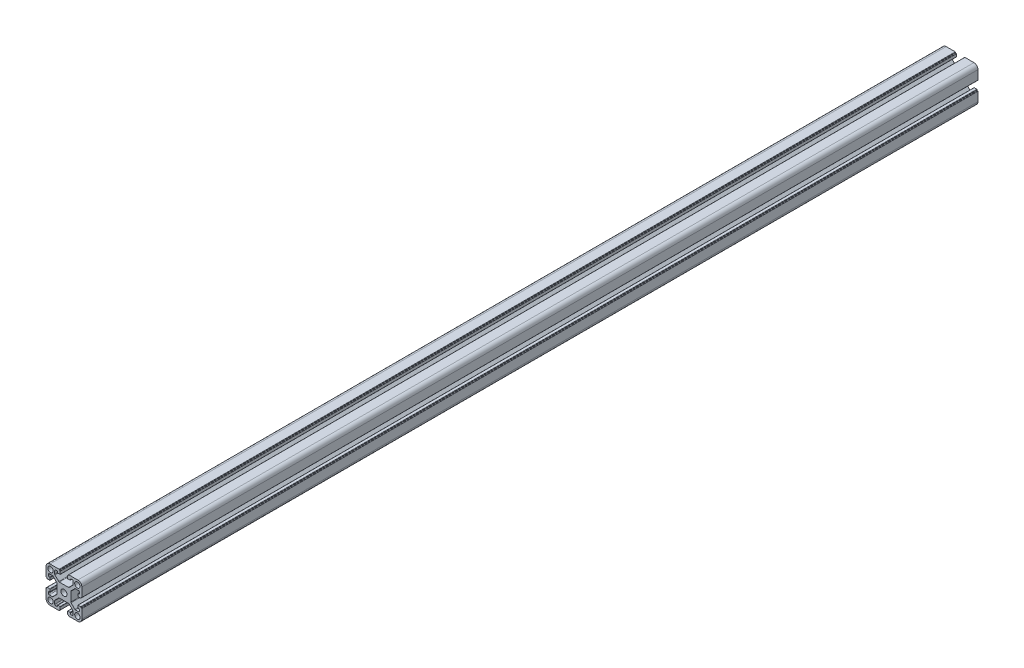
SolidWorks part; units mm, degrees
material "6063 T5"
ref_plane "Спереди" through (0, 0, 0) normal (0, 0, 1) x (1, 0, 0)
ref_plane "Сверху" through (0, 0, 0) normal (0, 1, 0) x (1, 0, 0)
ref_plane "Справа" through (0, 0, 0) normal (1, 0, 0) x (0, 0, -1)
sketch "Эскиз1" plane through (0, 0, 0) normal (0, 0, 1) x (1, 0, 0)
  line L0 (-19.98, 20.5457) -> (20.02, 20.5457) construction
  line L1 (-20, 10.25) -> (-20, 15.5)
  line L2 (-15.5, 20) -> (-10.25, 20)
  line L3 (10.25, 20) -> (15.5, 20)
  line L8 (20, 15.5) -> (20, 10.25)
  line L13 (20, -10.25) -> (20, -15.5)
  line L14 (15.5, -20) -> (10.25, -20)
  line L19 (-10.25, -20) -> (-15.5, -20)
  line L20 (-20, -15.5) -> (-20, -10.25)
  line L26 (-20.0124, 26.0326) -> (19.9876, 26.0326) construction
  arc A0 (-20, 15.5) -> (-15.5, 20) centre (-15.5, 15.5) cw
  circle A5 centre (0, 0) radius 3.4
  arc A6 (15.5, 20) -> (20, 15.5) centre (15.5, 15.5) cw
  circle A11 centre (15, 15) radius 3
  arc A16 (20, -15.5) -> (15.5, -20) centre (15.5, -15.5) cw
  circle A33 centre (-15, 15) radius 3
  circle A34 centre (15, -15) radius 3
  arc A35 (-15.5, -20) -> (-20, -15.5) centre (-15.5, -15.5) cw
  circle A36 centre (-15, -15) radius 3
  point P5 (0, 0)
  point P38 (0, 0)
  line B0 (-20, 10.25) -> (-20, 5.4)
  line B1 (-19.7, 5.1) -> (-19.3, 5.1)
  line B2 (-19, 4.8) -> (-19, 4.4)
  line B3 (-18.7, 4.1) -> (-15.8, 4.1)
  line B4 (-15.5, 4.4) -> (-15.5, 6.8)
  line B5 (-15.8, 7.1) -> (-16.3, 7.1)
  line B6 (-17.3, 8.1) -> (-17.3, 9.25)
  line B7 (-16.3, 10.25) -> (-12.8642, 10.25)
  line B8 (-12.1571, 9.9571) -> (-7.9929, 5.7929)
  line B9 (-7.7, 5.0858) -> (-7.7, -5.0858)
  line B10 (-7.7, 0) -> (-20, 0) construction
  line B11 (-12.1571, -9.9571) -> (-7.9929, -5.7929)
  line B12 (-16.3, -10.25) -> (-12.8642, -10.25)
  line B13 (-17.3, -8.1) -> (-17.3, -9.25)
  line B14 (-15.8, -7.1) -> (-16.3, -7.1)
  line B15 (-15.5, -4.4) -> (-15.5, -6.8)
  line B16 (-18.7, -4.1) -> (-15.8, -4.1)
  line B17 (-19, -4.8) -> (-19, -4.4)
  line B18 (-19.7, -5.1) -> (-19.3, -5.1)
  line B19 (-20, -10.25) -> (-20, -5.4)
  arc B20 (-15.5, 6.8) -> (-15.8, 7.1) centre (-15.8, 6.8) ccw
  arc B21 (-15.8, 4.1) -> (-15.5, 4.4) centre (-15.8, 4.4) ccw
  arc B22 (-19, 4.4) -> (-18.7, 4.1) centre (-18.7, 4.4) ccw
  arc B23 (-19.3, 5.1) -> (-19, 4.8) centre (-19.3, 4.8) cw
  arc B24 (-20, 5.4) -> (-19.7, 5.1) centre (-19.7, 5.4) ccw
  arc B25 (-7.9929, 5.7929) -> (-7.7, 5.0858) centre (-8.7, 5.0858) cw
  arc B26 (-12.8642, 10.25) -> (-12.1571, 9.9571) centre (-12.8642, 9.25) cw
  arc B27 (-17.3, 9.25) -> (-16.3, 10.25) centre (-16.3, 9.25) cw
  arc B28 (-16.3, 7.1) -> (-17.3, 8.1) centre (-16.3, 8.1) cw
  arc B29 (-16.3, -7.1) -> (-17.3, -8.1) centre (-16.3, -8.1) ccw
  arc B30 (-17.3, -9.25) -> (-16.3, -10.25) centre (-16.3, -9.25) ccw
  arc B31 (-12.8642, -10.25) -> (-12.1571, -9.9571) centre (-12.8642, -9.25) ccw
  arc B32 (-7.9929, -5.7929) -> (-7.7, -5.0858) centre (-8.7, -5.0858) ccw
  arc B33 (-20, -5.4) -> (-19.7, -5.1) centre (-19.7, -5.4) cw
  arc B34 (-19.3, -5.1) -> (-19, -4.8) centre (-19.3, -4.8) ccw
  arc B35 (-19, -4.4) -> (-18.7, -4.1) centre (-18.7, -4.4) cw
  arc B36 (-15.8, -4.1) -> (-15.5, -4.4) centre (-15.8, -4.4) cw
  arc B37 (-15.5, -6.8) -> (-15.8, -7.1) centre (-15.8, -6.8) cw
  line B38 (10.25, 20) -> (5.4, 20)
  line B39 (5.1, 19.7) -> (5.1, 19.3)
  line B40 (4.8, 19) -> (4.4, 19)
  line B41 (4.1, 18.7) -> (4.1, 15.8)
  line B42 (4.4, 15.5) -> (6.8, 15.5)
  line B43 (7.1, 15.8) -> (7.1, 16.3)
  line B44 (8.1, 17.3) -> (9.25, 17.3)
  line B45 (10.25, 16.3) -> (10.25, 12.8642)
  line B46 (9.9571, 12.1571) -> (5.7929, 7.9929)
  line B47 (5.0858, 7.7) -> (-5.0858, 7.7)
  line B48 (0, 7.7) -> (0, 20) construction
  line B49 (-9.9571, 12.1571) -> (-5.7929, 7.9929)
  line B50 (-10.25, 16.3) -> (-10.25, 12.8642)
  line B51 (-8.1, 17.3) -> (-9.25, 17.3)
  line B52 (-7.1, 15.8) -> (-7.1, 16.3)
  line B53 (-4.4, 15.5) -> (-6.8, 15.5)
  line B54 (-4.1, 18.7) -> (-4.1, 15.8)
  line B55 (-4.8, 19) -> (-4.4, 19)
  line B56 (-5.1, 19.7) -> (-5.1, 19.3)
  line B57 (-10.25, 20) -> (-5.4, 20)
  arc B58 (6.8, 15.5) -> (7.1, 15.8) centre (6.8, 15.8) ccw
  arc B59 (4.1, 15.8) -> (4.4, 15.5) centre (4.4, 15.8) ccw
  arc B60 (4.4, 19) -> (4.1, 18.7) centre (4.4, 18.7) ccw
  arc B61 (5.1, 19.3) -> (4.8, 19) centre (4.8, 19.3) cw
  arc B62 (5.4, 20) -> (5.1, 19.7) centre (5.4, 19.7) ccw
  arc B63 (5.7929, 7.9929) -> (5.0858, 7.7) centre (5.0858, 8.7) cw
  arc B64 (10.25, 12.8642) -> (9.9571, 12.1571) centre (9.25, 12.8642) cw
  arc B65 (9.25, 17.3) -> (10.25, 16.3) centre (9.25, 16.3) cw
  arc B66 (7.1, 16.3) -> (8.1, 17.3) centre (8.1, 16.3) cw
  arc B67 (-7.1, 16.3) -> (-8.1, 17.3) centre (-8.1, 16.3) ccw
  arc B68 (-9.25, 17.3) -> (-10.25, 16.3) centre (-9.25, 16.3) ccw
  arc B69 (-10.25, 12.8642) -> (-9.9571, 12.1571) centre (-9.25, 12.8642) ccw
  arc B70 (-5.7929, 7.9929) -> (-5.0858, 7.7) centre (-5.0858, 8.7) ccw
  arc B71 (-5.4, 20) -> (-5.1, 19.7) centre (-5.4, 19.7) cw
  arc B72 (-5.1, 19.3) -> (-4.8, 19) centre (-4.8, 19.3) ccw
  arc B73 (-4.4, 19) -> (-4.1, 18.7) centre (-4.4, 18.7) cw
  arc B74 (-4.1, 15.8) -> (-4.4, 15.5) centre (-4.4, 15.8) cw
  arc B75 (-6.8, 15.5) -> (-7.1, 15.8) centre (-6.8, 15.8) cw
  line B76 (20, -10.25) -> (20, -5.4)
  line B77 (19.7, -5.1) -> (19.3, -5.1)
  line B78 (19, -4.8) -> (19, -4.4)
  line B79 (18.7, -4.1) -> (15.8, -4.1)
  line B80 (15.5, -4.4) -> (15.5, -6.8)
  line B81 (15.8, -7.1) -> (16.3, -7.1)
  line B82 (17.3, -8.1) -> (17.3, -9.25)
  line B83 (16.3, -10.25) -> (12.8642, -10.25)
  line B84 (12.1571, -9.9571) -> (7.9929, -5.7929)
  line B85 (7.7, -5.0858) -> (7.7, 5.0858)
  line B86 (7.7, 0) -> (20, 0) construction
  line B87 (12.1571, 9.9571) -> (7.9929, 5.7929)
  line B88 (16.3, 10.25) -> (12.8642, 10.25)
  line B89 (17.3, 8.1) -> (17.3, 9.25)
  line B90 (15.8, 7.1) -> (16.3, 7.1)
  line B91 (15.5, 4.4) -> (15.5, 6.8)
  line B92 (18.7, 4.1) -> (15.8, 4.1)
  line B93 (19, 4.8) -> (19, 4.4)
  line B94 (19.7, 5.1) -> (19.3, 5.1)
  line B95 (20, 10.25) -> (20, 5.4)
  arc B96 (15.5, -6.8) -> (15.8, -7.1) centre (15.8, -6.8) ccw
  arc B97 (15.8, -4.1) -> (15.5, -4.4) centre (15.8, -4.4) ccw
  arc B98 (19, -4.4) -> (18.7, -4.1) centre (18.7, -4.4) ccw
  arc B99 (19.3, -5.1) -> (19, -4.8) centre (19.3, -4.8) cw
  arc B100 (20, -5.4) -> (19.7, -5.1) centre (19.7, -5.4) ccw
  arc B101 (7.9929, -5.7929) -> (7.7, -5.0858) centre (8.7, -5.0858) cw
  arc B102 (12.8642, -10.25) -> (12.1571, -9.9571) centre (12.8642, -9.25) cw
  arc B103 (17.3, -9.25) -> (16.3, -10.25) centre (16.3, -9.25) cw
  arc B104 (16.3, -7.1) -> (17.3, -8.1) centre (16.3, -8.1) cw
  arc B105 (16.3, 7.1) -> (17.3, 8.1) centre (16.3, 8.1) ccw
  arc B106 (17.3, 9.25) -> (16.3, 10.25) centre (16.3, 9.25) ccw
  arc B107 (12.8642, 10.25) -> (12.1571, 9.9571) centre (12.8642, 9.25) ccw
  arc B108 (7.9929, 5.7929) -> (7.7, 5.0858) centre (8.7, 5.0858) ccw
  arc B109 (20, 5.4) -> (19.7, 5.1) centre (19.7, 5.4) cw
  arc B110 (19.3, 5.1) -> (19, 4.8) centre (19.3, 4.8) ccw
  arc B111 (19, 4.4) -> (18.7, 4.1) centre (18.7, 4.4) cw
  arc B112 (15.8, 4.1) -> (15.5, 4.4) centre (15.8, 4.4) cw
  arc B113 (15.5, 6.8) -> (15.8, 7.1) centre (15.8, 6.8) cw
  line B114 (-10.25, -20) -> (-5.4, -20)
  line B115 (-5.1, -19.7) -> (-5.1, -19.3)
  line B116 (-4.8, -19) -> (-4.4, -19)
  line B117 (-4.1, -18.7) -> (-4.1, -15.8)
  line B118 (-4.4, -15.5) -> (-6.8, -15.5)
  line B119 (-7.1, -15.8) -> (-7.1, -16.3)
  line B120 (-8.1, -17.3) -> (-9.25, -17.3)
  line B121 (-10.25, -16.3) -> (-10.25, -12.8642)
  line B122 (-9.9571, -12.1571) -> (-5.7929, -7.9929)
  line B123 (-5.0858, -7.7) -> (5.0858, -7.7)
  line B124 (0, -7.7) -> (0, -20) construction
  line B125 (9.9571, -12.1571) -> (5.7929, -7.9929)
  line B126 (10.25, -16.3) -> (10.25, -12.8642)
  line B127 (8.1, -17.3) -> (9.25, -17.3)
  line B128 (7.1, -15.8) -> (7.1, -16.3)
  line B129 (4.4, -15.5) -> (6.8, -15.5)
  line B130 (4.1, -18.7) -> (4.1, -15.8)
  line B131 (4.8, -19) -> (4.4, -19)
  line B132 (5.1, -19.7) -> (5.1, -19.3)
  line B133 (10.25, -20) -> (5.4, -20)
  arc B134 (-6.8, -15.5) -> (-7.1, -15.8) centre (-6.8, -15.8) ccw
  arc B135 (-4.1, -15.8) -> (-4.4, -15.5) centre (-4.4, -15.8) ccw
  arc B136 (-4.4, -19) -> (-4.1, -18.7) centre (-4.4, -18.7) ccw
  arc B137 (-5.1, -19.3) -> (-4.8, -19) centre (-4.8, -19.3) cw
  arc B138 (-5.4, -20) -> (-5.1, -19.7) centre (-5.4, -19.7) ccw
  arc B139 (-5.7929, -7.9929) -> (-5.0858, -7.7) centre (-5.0858, -8.7) cw
  arc B140 (-10.25, -12.8642) -> (-9.9571, -12.1571) centre (-9.25, -12.8642) cw
  arc B141 (-9.25, -17.3) -> (-10.25, -16.3) centre (-9.25, -16.3) cw
  arc B142 (-7.1, -16.3) -> (-8.1, -17.3) centre (-8.1, -16.3) cw
  arc B143 (7.1, -16.3) -> (8.1, -17.3) centre (8.1, -16.3) ccw
  arc B144 (9.25, -17.3) -> (10.25, -16.3) centre (9.25, -16.3) ccw
  arc B145 (10.25, -12.8642) -> (9.9571, -12.1571) centre (9.25, -12.8642) ccw
  arc B146 (5.7929, -7.9929) -> (5.0858, -7.7) centre (5.0858, -8.7) ccw
  arc B147 (5.4, -20) -> (5.1, -19.7) centre (5.4, -19.7) cw
  arc B148 (5.1, -19.3) -> (4.8, -19) centre (4.8, -19.3) ccw
  arc B149 (4.4, -19) -> (4.1, -18.7) centre (4.4, -18.7) cw
  arc B150 (4.1, -15.8) -> (4.4, -15.5) centre (4.4, -15.8) cw
  arc B151 (6.8, -15.5) -> (7.1, -15.8) centre (6.8, -15.8) cw
  dimension "D2" = 4.5
  dimension "D3" = 6
  dimension "D5" = 15
  dimension "D6" = 6.8
  dimension "D4" = 15
  dimension "D1" = 20
  dimension "D7" = 40
  dimension "D8" = 4
sketch_block_instance "8B(20,5PL)-1"
sketch_block "8B(20,5PL)" parameters "D7"=0.3, "D8"=1, "D1"=12.3, "D2"=4.5, "D3"=8.2, "D4"=20.5, "D5"=10.2, "D6"=135, "D9"=11.8, "D10"=4.85, "D11"=1.65, "D12"=0.6
sketch_block_instance "8B(20,5PL)-3"
sketch_block_instance "8B(20,5PL)-4"
sketch_block_instance "8B(20,5PL)-5"
extrude "Бобышка-Вытянуть1" add sketch "Эскиз1" along normal blind 1000
